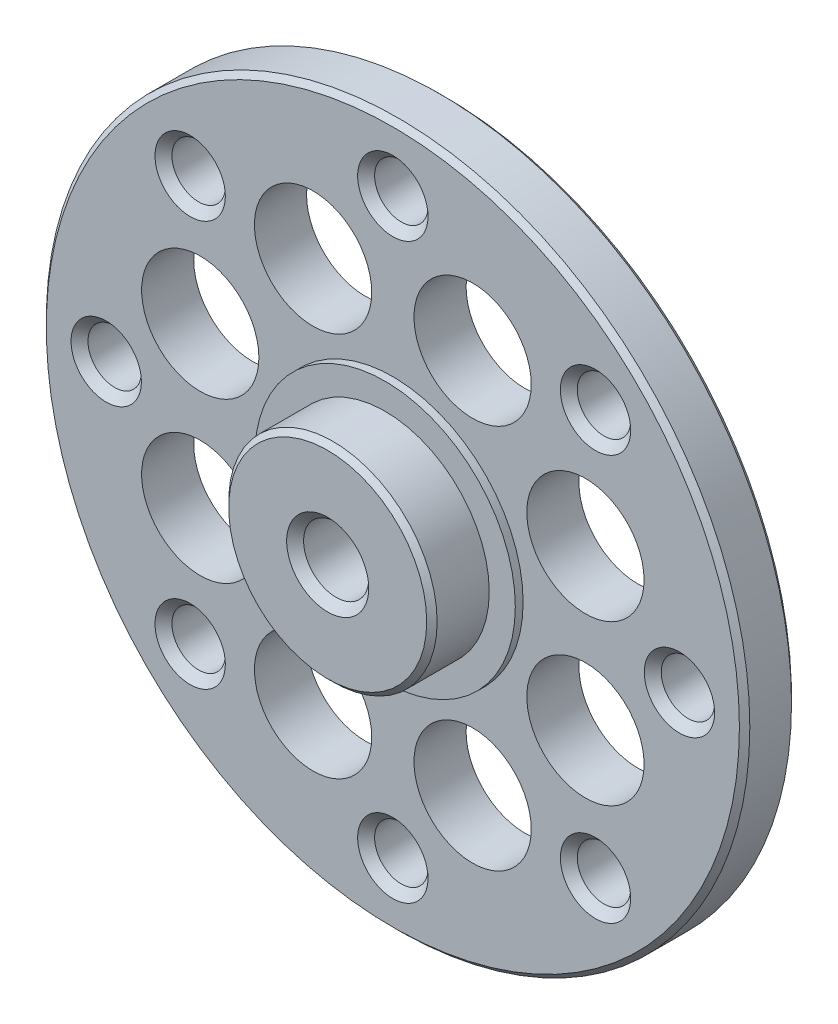
SolidWorks part; units mm, degrees
material "1060 Alloy"
ref_plane "Front Plane" through (0, 0, 0) normal (0, 0, 1) x (1, 0, 0)
ref_plane "Top Plane" through (0, 0, 0) normal (0, 1, 0) x (1, 0, 0)
ref_plane "Right Plane" through (0, 0, 0) normal (1, 0, 0) x (0, 0, -1)
sketch "Sketch1" plane through (0, 0, 0) normal (0, 1, 0) x (1, 0, 0)
  line L0 (13.5, 0) -> (0, 0)
  line L1 (0, 0) -> (0, -2)
  line L2 (0, -2) -> (13.5, -2)
  line L3 (13.5, -2) -> (13.5, 0)
  line L4 (0, 0) -> (0, -2) construction
revolve "Revolve1" add sketch "Sketch1" angle 360 about L4
sketch "Sketch2" plane through (0, 0, 2) normal (0, 0, 1) x (1, 0, 0)
  circle A0 centre (0, 0) radius 5
extrude "Boss-Extrude1" add sketch "Sketch2" along normal blind 0.3
sketch "Sketch3" plane through (0, 0, 2.3) normal (0, 0, 1) x (1, 0, 0)
  circle A0 centre (0, 0) radius 4
extrude "Boss-Extrude2" add sketch "Sketch3" along normal blind 2.2
sketch "Sketch4" plane through (0, 0, 0) normal (0, 0, -1) x (-1, 0, 0)
  circle A0 centre (0, 0) radius 5
extrude "Boss-Extrude3" add sketch "Sketch4" along normal blind 0.5
hole_wizard "#8 Clearance Hole1" positions "Sketch6" profile "Sketch5" hole size "#8" standard "ANSI Inch"
sketch "Sketch6" plane through (0, 0, 2) normal (0, 0, 1) x (1, 0, 0)
  point P0 (3.0615, 7.391)
  point P1 (7.391, 3.0615)
  point P2 (7.391, -3.0615)
  point P3 (3.0615, -7.391)
  point P4 (-3.0615, -7.391)
  point P5 (-7.391, -3.0615)
  point P6 (-7.391, 3.0615)
  point P7 (-3.0615, 7.391)
sketch "Sketch5" plane through (3.0615, 7.391, 2) normal (1, 0, 0) x (0, -1, 0)
  line L0 (0, 0) -> (0, 2.5)
  line L1 (0, 2.5) -> (2.25, 2.5)
  line L2 (2.25, 2.5) -> (2.25, 0)
  line L5 (2.25, 0) -> (0, 0)
  line L11 (0, -6.35) -> (0, 107.95) construction
  dimension "Thru Hole Dia." = 4.5
  dimension "Thru Hole Depth" = 2.5
hole_wizard "#1 Clearance Hole1" positions "Sketch8" profile "Sketch7" hole size "#1" standard "ANSI Inch"
sketch "Sketch8" plane through (0, 0, 2) normal (0, 0, 1) x (1, 0, 0)
  point P0 (7.7782, 7.7782)
  point P1 (11, 0)
  point P2 (7.7782, -7.7782)
  point P3 (0, -11)
  point P4 (-7.7782, -7.7782)
  point P5 (-11, 0)
  point P6 (-7.7782, 7.7782)
  point P7 (0, 11)
sketch "Sketch7" plane through (7.7782, 7.7782, 2) normal (1, 0, 0) x (0, -1, 0)
  line L0 (0, 0) -> (0, 2.5)
  line L1 (0, 2.5) -> (1.025, 2.5)
  line L2 (1.025, 2.5) -> (1.025, 0)
  line L5 (1.025, 0) -> (0, 0)
  line L11 (0, -6.35) -> (0, 107.95) construction
  dimension "Thru Hole Dia." = 2.05
  dimension "Thru Hole Depth" = 2.5
hole_wizard "#2 Clearance Hole1" positions "Sketch10" profile "Sketch9" hole size "#2" standard "ANSI Inch"
sketch "Sketch10" plane through (0, 0, 4.5) normal (0, 0, 1) x (1, 0, 0)
  point P0 (0, 0)
sketch "Sketch9" plane through (0, 0, 4.5) normal (1, 0, 0) x (0, -1, 0)
  line L0 (0, 0) -> (0, 5)
  line L1 (0, 5) -> (1.25, 5)
  line L2 (1.25, 5) -> (1.25, 0)
  line L5 (1.25, 0) -> (0, 0)
  line L11 (0, -6.35) -> (0, 107.95) construction
  dimension "Thru Hole Dia." = 2.5
  dimension "Thru Hole Depth" = 5
chamfer "Chamfer1" distance 0.325 angle 45 9 edges at (1.025, -11, 2) (1.025, 11, 2) (-9.975, 0, 2) (1.25, 0, 4.5) (-6.7532, -7.7782, 2) (-6.7532, 7.7782, 2) (8.8032, 7.7782, 2) (12.025, 0, 2) (8.8032, -7.7782, 2)
chamfer "Chamfer2" distance 0.2 angle 45 2 edges at (13.5, 0, 2) (13.5, 0, 0)
chamfer "Chamfer3" distance 0.2 angle 45 2 edges at (4, 0, 4.5) (-5, 0, -0.5)
